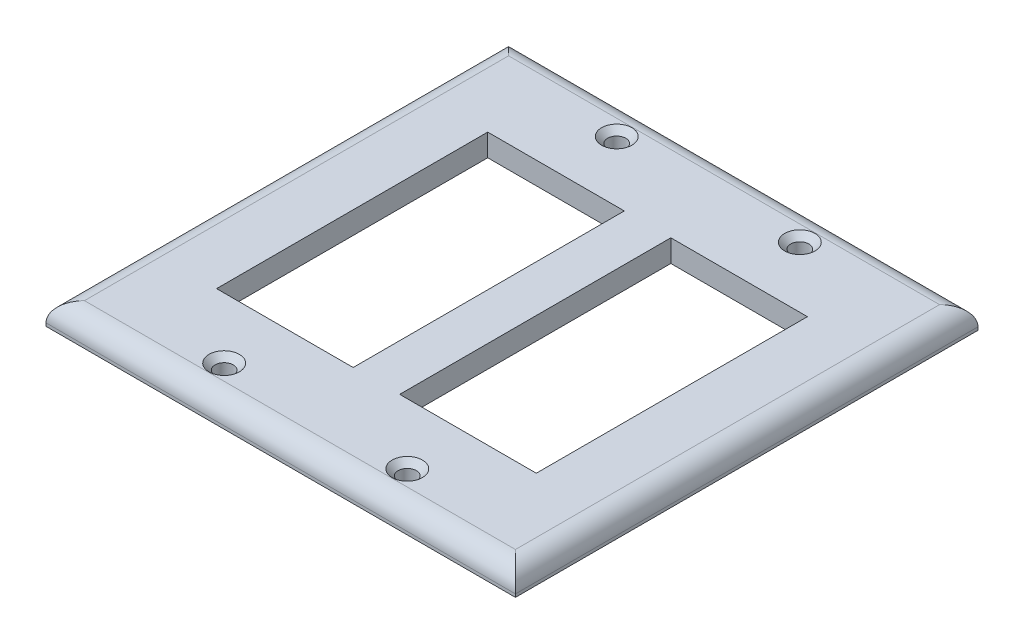
SolidWorks part; units mm, degrees
ref_plane "Front" through (0, 0, 0) normal (0, 0, 1) x (1, 0, 0)
ref_plane "Top" through (0, 0, 0) normal (0, 1, 0) x (1, 0, 0)
ref_plane "Right" through (0, 0, 0) normal (1, 0, 0) x (0, 0, -1)
sketch "Sketch1" plane through (0, 0, 0) normal (0, 1, 0) x (1, 0, 0)
  line L0 (-14.4996, 6.3229) -> (-14.4996, 21.3229)
  line L1 (-49.8746, 29.9729) -> (66.1254, 29.9729)
  line L2 (-49.8746, 29.9729) -> (-49.8746, -84.3271)
  line L3 (-49.8746, -84.3271) -> (66.1254, -84.3271)
  line L4 (66.1254, 29.9729) -> (66.1254, -84.3271)
  line L5 (-31.3746, 6.3229) -> (2.3754, 6.3229)
  line L6 (-31.3746, 6.3229) -> (-31.3746, -60.6771)
  line L7 (-31.3746, -60.6771) -> (2.3754, -60.6771)
  line L8 (2.3754, 6.3229) -> (2.3754, -60.6771)
  line L9 (13.8754, 6.3229) -> (47.6254, 6.3229)
  line L10 (13.8754, 6.3229) -> (13.8754, -60.6771)
  line L11 (13.8754, -60.6771) -> (47.6254, -60.6771)
  line L12 (47.6254, 6.3229) -> (47.6254, -60.6771)
  line L13 (-14.4996, -60.6771) -> (-14.4996, -75.6771)
  line L14 (30.7504, -60.6771) -> (30.7504, -75.6771)
  line L15 (30.7504, 6.3229) -> (30.7504, 21.3229)
  circle A0 centre (-14.4996, 21.3229) radius 2.25
  circle A1 centre (-14.4996, -75.6771) radius 2.25
  circle A2 centre (30.7504, -75.6771) radius 2.25
  circle A3 centre (30.7504, 21.3229) radius 2.25
  dimension "D10" = 4.5
  dimension "D1" = 116
  dimension "D2" = 114.3
  dimension "D3" = 33.75
  dimension "D4" = 67
  dimension "D5" = 23.65
  dimension "D6" = 18.5
  dimension "D7" = 18.5
  dimension "D8" = 23.65
  dimension "D9" = 15
extrude "Boss-Extrude1" add sketch "Sketch1" along normal blind 5.5 contours L4 L1 L2 L3 L5 L8 L7 L6 L9 L12 L11 L10 | L8 L5 L6 L7
fillet "Fillet1" radius 4.75 4 edges at (-49.8746, 5.5, 27.1771) (8.1254, 5.5, 84.3271) (66.1254, 5.5, 27.1771) (8.1254, 5.5, -29.9729)
chamfer "Chamfer1" distance 1.5 angle 45 4 edges at (30.7504, 5.5, 77.9271) (-14.4996, 5.5, 77.9271) (30.7504, 5.5, -19.0729) (-14.4996, 5.5, -19.0729)
